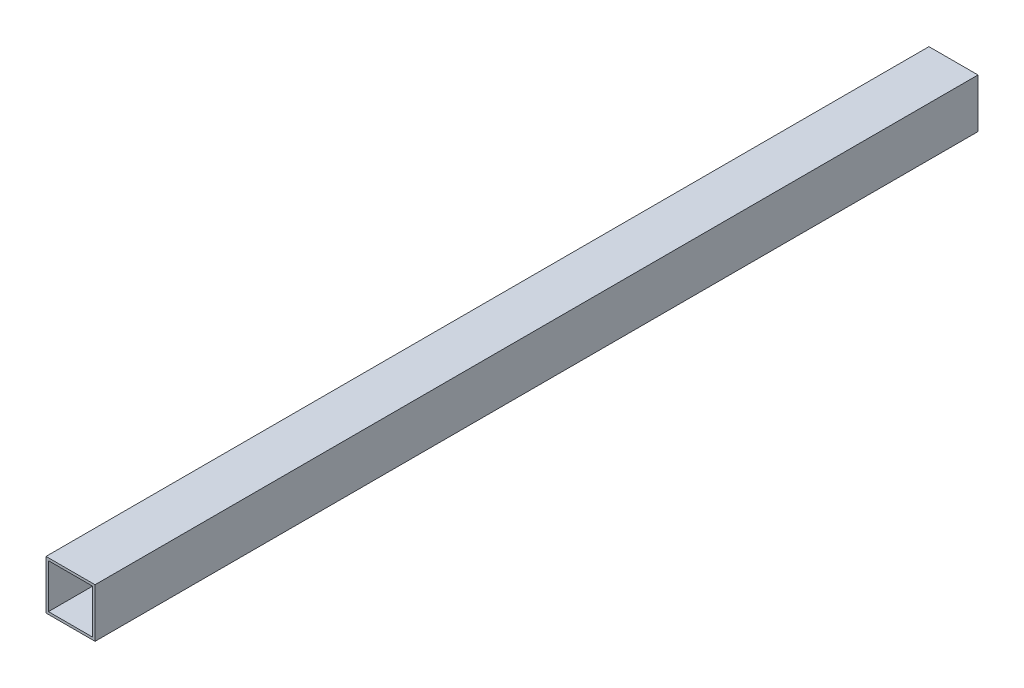
SolidWorks part; units mm, degrees
ref_plane "Front Plane" through (0, 0, 0) normal (0, 0, 1) x (1, 0, 0)
ref_plane "Top Plane" through (0, 0, 0) normal (0, 1, 0) x (1, 0, 0)
ref_plane "Right Plane" through (0, 0, 0) normal (1, 0, 0) x (0, 0, -1)
sketch "Sketch1" plane through (0, 0, 0) normal (0, 0, 1) x (1, 0, 0)
  line L1 (0, 0) -> (20, 0)
  line L2 (0, 0) -> (0, -20)
  line L3 (0, -20) -> (20, -20)
  line L4 (20, 0) -> (20, -20)
  line L5 (1, -19) -> (19, -19)
  line L6 (1, -19) -> (1, -1)
  line L7 (1, -1) -> (19, -1)
  line L8 (19, -19) -> (19, -1)
  line L9 (1, -19) -> (19, -1) construction
  line L10 (1, -1) -> (19, -19) construction
  point P5 (10, -10)
  dimension "D1" = 20
  dimension "D2" = 20
  dimension "D3" = 1
  dimension "D4" = 1
  dimension "D5" = 1
  dimension "D6" = 1
extrude "Boss-Extrude1" add sketch "Sketch1" along normal blind 360
